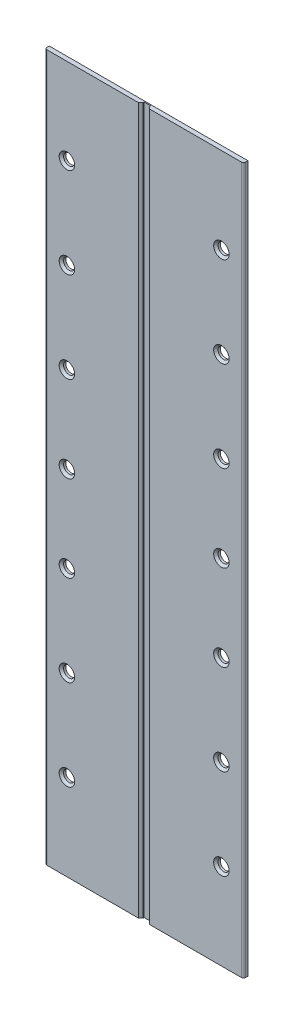
SolidWorks part; units mm, degrees
ref_plane "Plan de face" through (0, 0, 0) normal (0, 0, 1) x (1, 0, 0)
ref_plane "Plan de dessus" through (0, 0, 0) normal (0, 1, 0) x (1, 0, 0)
ref_plane "Plan de droite" through (0, 0, 0) normal (1, 0, 0) x (0, 0, -1)
sketch "Esquisse1" plane through (0, 0, 0) normal (0, 0, 1) x (1, 0, 0)
  line L1 (45, 160) -> (-45, 160)
  line L2 (45, 160) -> (45, -160)
  line L3 (45, -160) -> (-45, -160)
  line L4 (-45, 160) -> (-45, -160)
  line L5 (45, 160) -> (-45, -160) construction
  line L6 (45, -160) -> (-45, 160) construction
  point P0 (0, 0)
  dimension "D1" = 320
  dimension "D2" = 90
extrude "Boss.-Extru.1" add sketch "Esquisse1" along normal blind 2
sketch "Esquisse2" plane through (0, 0, 2) normal (0, 0, 1) x (1, 0, 0)
  line L0 (45, 160) -> (35, 160)
  line L1 (45, 160) -> (-45, 160) construction
  line L2 (-15.0203, 0) -> (15.0203, 0) construction
  line L4 (35, -80) -> (61.6015, -80) construction
  line L5 (0, 0) -> (0, 26.6297) construction
  line L7 (-35, -80) -> (-61.6015, -80) construction
  circle A0 centre (35, 0) radius 2.5
  circle A1 centre (35, 80) radius 2.5
  circle A2 centre (35, -80) radius 2.5
  circle A3 centre (35, -120.982) radius 2.5
  circle A4 centre (35, 120.982) radius 2.5
  circle A5 centre (35, -39.018) radius 2.5
  circle A6 centre (35, 39.018) radius 2.5
  circle A7 centre (35, 80) radius 2.5
  circle A8 centre (-35, -39.018) radius 2.5
  circle A9 centre (-35, -120.982) radius 2.5
  circle A10 centre (-35, -80) radius 2.5
  circle A11 centre (-35, 0) radius 2.5
  circle A12 centre (-35, 80) radius 2.5
  circle A13 centre (-35, 39.018) radius 2.5
  circle A14 centre (-35, 120.982) radius 2.5
  circle A15 centre (-35, 80) radius 2.5
  dimension "D1" = 10
extrude "Enlèv. mat.-Extru.1" cut sketch "Esquisse2" against normal blind 45 contours A14 | A4 | A1 | A12 | A13 | A6 | A0 | A11 | A8 | A5 | A2 | A10 | A3 | A9
fillet "Congé2" radius 1 2 edges at (-45, 0, 2) (45, 0, 2)
chamfer "Chanfrein1" distance 1 angle 45 14 edges at (37.5, 120.982, 2) (37.5, 80, 2) (37.5, 39.018, 2) (37.5, 0, 2) (37.5, -39.018, 2) (37.5, -80, 2) (37.5, -120.982, 2) (-32.5, 120.982, 2) (-32.5, 80, 2) (-32.5, 39.018, 2) (-32.5, 0, 2) (-32.5, -39.018, 2) (-32.5, -80, 2) (-32.5, -120.982, 2)
sketch "Esquisse3" plane through (0, 0, 0) normal (0, 0, 1) x (1, 0, 0)
  line L0 (0, 0) -> (0, -160) construction
  line L1 (-44, -160) -> (44, -160) construction
  line L2 (1.5, -160) -> (-1.5, -160)
  line L3 (-1.5, -160) -> (-1.5, 160)
  line L4 (44, 160) -> (-44, 160) construction
  line L5 (-1.5, 160) -> (1.5, 160)
  line L6 (1.5, 160) -> (1.5, -160)
  point P8 (0, -160)
  dimension "D1" = 3
extrude "Enlèv. mat.-Extru.2" cut sketch "Esquisse3" against normal blind 1.5 from surface at 2 starting at face at (31.5, 120.982, 2)
chamfer "Chanfrein2" distance 1 angle 45 2 edges at (1.5, 0, 2) (-1.5, 0, 2)
